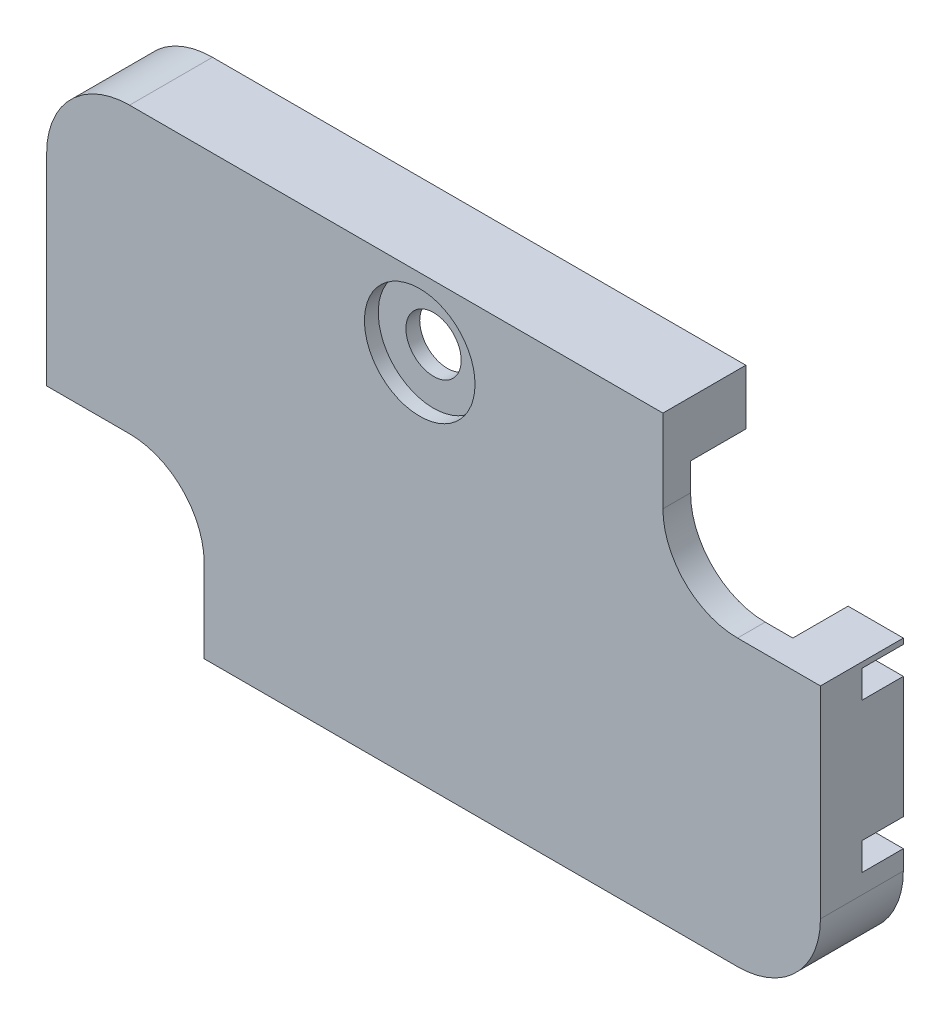
SolidWorks part; units mm, degrees
material "PA Typ 6"
ref_plane "Płaszczyzna przednia" through (0, 0, 0) normal (0, 0, 1) x (1, 0, 0)
ref_plane "Płaszczyzna górna" through (0, 0, 0) normal (0, 1, 0) x (1, 0, 0)
ref_plane "Płaszczyzna prawa" through (0, 0, 0) normal (1, 0, 0) x (0, 0, -1)
sketch "Szkic1" plane through (0, 0, 0) normal (0, 0, 1) x (1, 0, 0)
  line L4 (-11, 8) -> (8.3, 8)
  line L5 (-14, -2.3) -> (-14, 5)
  line L6 (14, 2.3) -> (14, -5)
  line L7 (11, -8) -> (-8.3, -8)
  line L8 (-8.3, -5) -> (-8.3, -8)
  line L9 (-11, -2.3) -> (-14, -2.3)
  line L10 (8.3, 5) -> (8.3, 8)
  line L11 (11, 2.3) -> (14, 2.3)
  arc A10 (-8.3, -5) -> (-11, -2.3) centre (-11, -5) ccw
  arc A13 (8.3, 5) -> (11, 2.3) centre (11, 5) ccw
  arc A15 (-11, 8) -> (-14, 5) centre (-11, 5) ccw
  arc A16 (11, -8) -> (14, -5) centre (11, -5) ccw
extrude "Dodanie-wyciągnięcie1" add sketch "Szkic1" along normal blind 3
sketch "Szkic2" plane through (0, 0, 0) normal (0, 0, -1) x (-1, 0, 0)
  line L0 (11, 7) -> (-7.3, 7)
  line L1 (-13, 1.3) -> (-13, -5)
  line L2 (-11, -7) -> (7.3, -7)
  line L3 (-8.3, 5) -> (-8.3, 6)
  line L4 (13, -1.3) -> (13, 5)
  line L5 (-11, 2.3) -> (-12, 2.3)
  line L6 (8.3, -5) -> (8.3, -6)
  line L7 (11, -2.3) -> (12, -2.3)
  arc A0 (-11, 2.3) -> (-8.3, 5) centre (-11, 5) ccw
  arc A1 (11, -2.3) -> (8.3, -5) centre (11, -5) ccw
  arc A2 (13, 5) -> (11, 7) centre (11, 5) ccw
  arc A3 (12, -2.3) -> (13, -1.3) centre (12, -1.3) ccw
  arc A4 (-13, -5) -> (-11, -7) centre (-11, -5) ccw
  arc A5 (8.3, -6) -> (7.3, -7) centre (7.3, -6) cw
  arc A6 (-12, 2.3) -> (-13, 1.3) centre (-12, 1.3) ccw
  arc A7 (-7.3, 7) -> (-8.3, 6) centre (-7.3, 6) ccw
extrude "Wytnij-wyciągnięcie1" cut sketch "Szkic2" against normal blind 2
sketch "Szkic3" plane through (14, 0, 0) normal (1, 0, 0) x (0, 0, -1)
  line L0 (0, -5) -> (0, 2.3) construction
  line L1 (0, 2.1) -> (-1.5, 2.1)
  line L2 (0, 2.1) -> (0, 1.1)
  line L3 (0, 1.1) -> (-1.5, 1.1)
  line L4 (-1.5, 2.1) -> (-1.5, 1.1)
  line L5 (5, 2.1) -> (0, 2.1) construction
  line L6 (5, -3.3) -> (0, -3.3) construction
  line L7 (0, -3.3) -> (-1.5, -3.3)
  line L8 (0, -3.3) -> (0, -4.3)
  line L9 (0, -4.3) -> (-1.5, -4.3)
  line L10 (-1.5, -3.3) -> (-1.5, -4.3)
  line L11 (0, 1.1) -> (5, 1.1) construction
  dimension "D1" = 1.5
extrude "Wytnij-wyciągnięcie2" cut sketch "Szkic3" against normal up to next
sketch "Szkic4" plane through (0, -8, 0) normal (0, -1, 0) x (1, 0, 0)
  line L0 (-8.3, 0) -> (11, 0) construction
  line L1 (1.5, 0) -> (2.5, 0)
  line L2 (1.5, 0) -> (1.5, 1.5)
  line L3 (1.5, 1.5) -> (2.5, 1.5)
  line L4 (2.5, 0) -> (2.5, 1.5)
  line L5 (1.5, 0) -> (1.5, -5) construction
  dimension "D1" = 1
  dimension "D2" = 1.5
extrude "Wytnij-wyciągnięcie3" cut sketch "Szkic4" against normal up to next
sketch "Szkic5" plane through (0, 0, 3) normal (0, 0, 1) x (1, 0, 0)
  circle A0 centre (-0.5, 5.5) radius 2 construction
  circle A1 centre (-0.5, 5.5) radius 2
extrude "Wytnij-wyciągnięcie4" cut sketch "Szkic5" against normal blind 0.5
sketch "Szkic6" plane through (0, 0, 2.5) normal (0, 0, 1) x (1, 0, 0)
  circle A0 centre (-0.5, 5.5) radius 1 construction
  circle A1 centre (-0.5, 5.5) radius 1
extrude "Wytnij-wyciągnięcie5" cut sketch "Szkic6" against normal up to next
